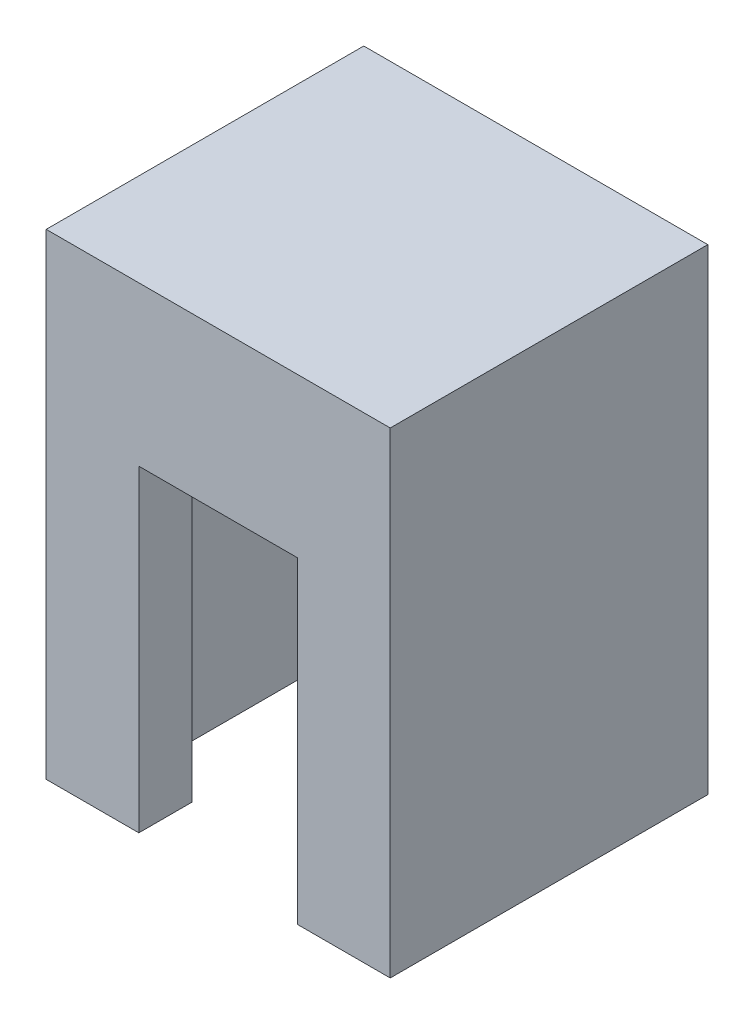
SolidWorks part; units mm, degrees
ref_plane "Plan de face" through (0, 0, 0) normal (0, 0, 1) x (1, 0, 0)
ref_plane "Plan de dessus" through (0, 0, 0) normal (0, 1, 0) x (1, 0, 0)
ref_plane "Plan de droite" through (0, 0, 0) normal (1, 0, 0) x (0, 0, -1)
sketch "Esquisse1" plane through (0, 0, 0) normal (0, 0, 1) x (1, 0, 0)
  line L1 (-6.5, -9) -> (6.5, -9)
  line L2 (-6.5, -9) -> (-6.5, 9)
  line L3 (-6.5, 9) -> (6.5, 9)
  line L4 (6.5, -9) -> (6.5, 9)
  line L5 (-6.5, -9) -> (6.5, 9) construction
  line L6 (-6.5, 9) -> (6.5, -9) construction
  point P0 (0, 0)
  dimension "D1" = 13
  dimension "D2" = 18
extrude "Boss.-Extru.1" add sketch "Esquisse1" along normal blind 12
sketch "Esquisse2" plane through (0, -9, 0) normal (0, -1, 0) x (1, 0, 0)
  line L0 (0, 12) -> (0, 0) construction
  line L1 (-6.5, 12) -> (6.5, 12) construction
  line L2 (-6.5, 0) -> (6.5, 0) construction
  line L3 (-5, 10) -> (-3, 10)
  line L4 (-5, 2) -> (5, 2) construction
  line L5 (-5, 2) -> (-5, 10)
  line L6 (-5, 10) -> (5, 10) construction
  line L7 (5, 2) -> (5, 10)
  line L8 (-5, 2) -> (5, 10) construction
  line L9 (-5, 10) -> (5, 2) construction
  line L10 (5, 10) -> (3, 10)
  line L11 (-3, 10) -> (-3, 12)
  line L12 (-3, 12) -> (3, 12)
  line L13 (3, 12) -> (3, 10)
  line L14 (-6.5, 6) -> (6.5, 6) construction
  line L15 (-6.5, 12) -> (-6.5, 0) construction
  line L16 (6.5, 12) -> (6.5, 0) construction
  line L17 (-5, 2) -> (-3, 2)
  line L18 (5, 2) -> (3, 2)
  line L19 (3, 0) -> (3, 2)
  line L20 (-3, 0) -> (3, 0)
  line L21 (-3, 2) -> (-3, 0)
  point P6 (0, 6)
  dimension "D1" = 10
  dimension "D2" = 6
  dimension "D3" = 2
extrude "Enlèv. mat.-Extru.1" cut sketch "Esquisse2" against normal blind 12
